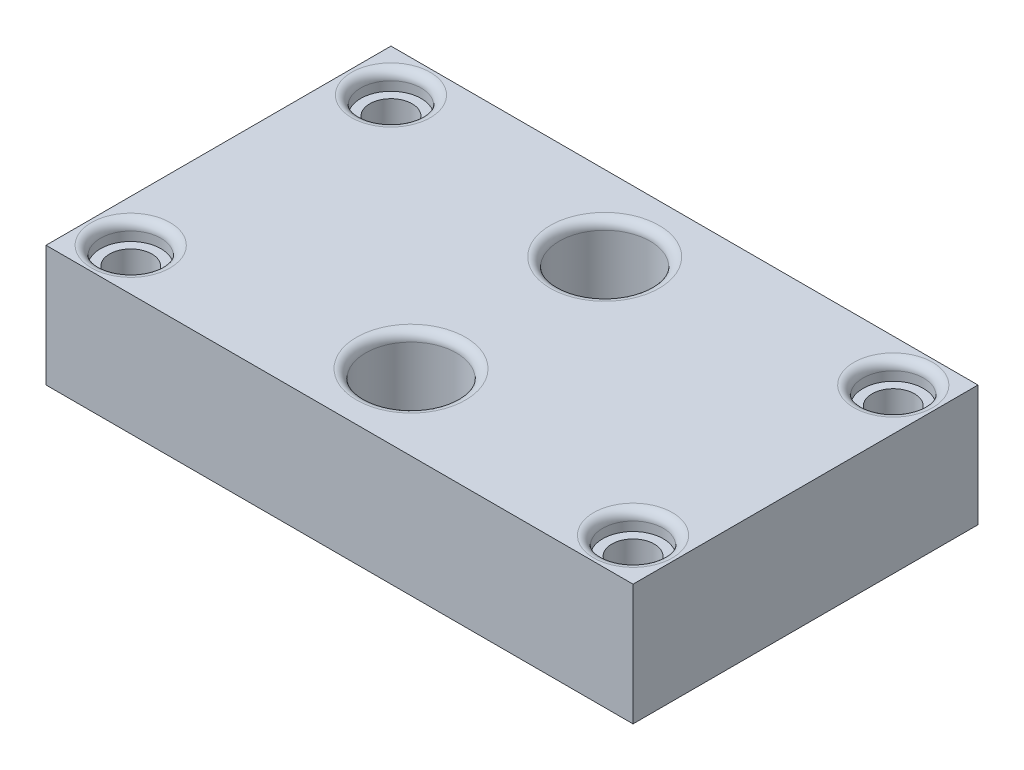
SolidWorks part; units mm, degrees
ref_plane "Front Plane" through (0, 0, 0) normal (0, 0, 1) x (1, 0, 0)
ref_plane "Top Plane" through (0, 0, 0) normal (0, 1, 0) x (1, 0, 0)
ref_plane "Right Plane" through (0, 0, 0) normal (1, 0, 0) x (0, 0, -1)
sketch "Sketch1" plane through (0, 515.9579, 0) normal (0, 1, 0) x (1, 0, 0)
  line L0 (-624.2594, 28.5) -> (-624.2594, -28.5)
  line L1 (-624.2594, -28.5) -> (-527.2594, -28.5)
  line L2 (-527.2594, -28.5) -> (-527.2594, 28.5)
  line L3 (-527.2594, 28.5) -> (-624.2594, 28.5)
  line L4 (-625.7594, 30) -> (-625.7594, -30)
  line L5 (-625.7594, -30) -> (-525.7594, -30)
  line L6 (-525.7594, -30) -> (-525.7594, 30)
  line L7 (-525.7594, 30) -> (-625.7594, 30)
  line L8 (-625.7594, 30) -> (-625.7594, -30) construction
  line L9 (-625.7594, -30) -> (-525.7594, -30) construction
  line L10 (-525.7594, -30) -> (-525.7594, 30) construction
  line L11 (-525.7594, 30) -> (-625.7594, 30) construction
  dimension "D1" = 0
  dimension "D2" = 1.5
extrude "Boss-Extrude1" add sketch "Sketch1" along normal blind 20
sketch "Sketch2" plane through (0, 535.9579, 0) normal (0, 1, 0) x (1, 0, 0)
  line L0 (-527.2594, -28.5) -> (-527.2594, 28.5) construction
  line L1 (-527.2594, 28.5) -> (-624.2594, 28.5) construction
  line L2 (-575.7594, 28.5) -> (-575.7594, -28.5) construction
  line L3 (-624.2594, -28.5) -> (-527.2594, -28.5) construction
  line L4 (-527.2594, 0) -> (-624.2594, 0) construction
  line L5 (-624.2594, 28.5) -> (-624.2594, -28.5) construction
  circle A2 centre (-534.2594, 21.5) radius 3.5
  circle A3 centre (-617.2594, 21.5) radius 3.5
  circle A5 centre (-534.2594, -21.5) radius 3.5
  circle A6 centre (-617.2594, -21.5) radius 3.5
  dimension "D1" = 7
  dimension "D2" = 7
  dimension "D4" = 7
  dimension "D5" = 7
  dimension "D6" = 7
  dimension "D3" = 7
extrude "Cut-Extrude1" cut sketch "Sketch2" against normal blind 10
sketch "Sketch3" plane through (0, 535.9579, 0) normal (0, 1, 0) x (1, 0, 0)
  circle A0 centre (-534.2594, 21.5) radius 5
  circle A1 centre (-617.2594, 21.5) radius 5
  circle A2 centre (-617.2594, -21.5) radius 5
  circle A3 centre (-534.2594, -21.5) radius 5
  dimension "D1" = 10
  dimension "D2" = 10
  dimension "D3" = 10
  dimension "D4" = 10
extrude "Cut-Extrude2" cut sketch "Sketch3" against normal blind 3
sketch "Sketch4" plane through (0, 535.9579, 0) normal (0, 1, 0) x (1, 0, 0)
  line L1 (-524.2795, 0) -> (-749.2795, 0) construction
  circle A0 centre (-576.4416, 16) radius 7.5
  circle A1 centre (-576.4416, -16) radius 7.5
  dimension "D1" = 15
  dimension "D2" = 15
  dimension "D3" = 32
  dimension "D4" = 16
extrude "Cut-Extrude3" cut sketch "Sketch4" against normal through all
fillet "Fillet1" radius 1.5 6 edges at (-617.2594, 535.9579, 26.5) (-617.2594, 535.9579, -16.5) (-534.2594, 535.9579, -16.5) (-534.2594, 535.9579, 26.5) (-576.4416, 535.9579, 23.5) (-576.4416, 535.9579, -8.5)
